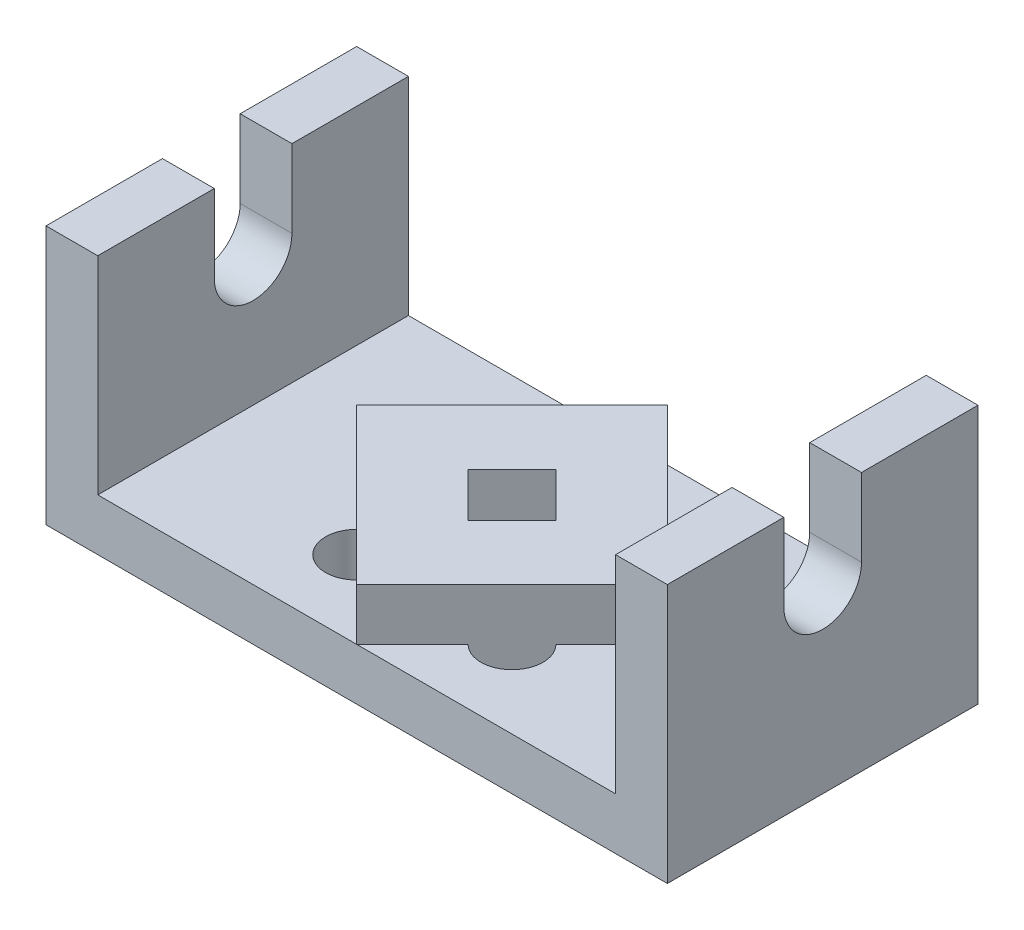
SolidWorks part; units mm, degrees
ref_plane "Front Plane" through (0, 0, 0) normal (0, 0, 1) x (1, 0, 0)
ref_plane "Top Plane" through (0, 0, 0) normal (0, 1, 0) x (1, 0, 0)
ref_plane "Right Plane" through (0, 0, 0) normal (1, 0, 0) x (0, 0, -1)
sketch "Sketch1" plane through (0, 0, 0) normal (0, 0, 1) x (1, 0, 0)
  line L0 (0, 44.72) -> (0, -57.36) construction
  line L1 (-92.16, 0) -> (92.8, 0) construction
  line L2 (-60, 0) -> (60, 0)
  line L3 (60, 0) -> (60, 50)
  line L4 (60, 50) -> (50, 50)
  line L5 (50, 50) -> (50, 10)
  line L6 (50, 10) -> (-50, 10)
  line L7 (-60, 50) -> (-50, 50)
  line L8 (-60, 0) -> (-60, 50)
  line L9 (-50, 50) -> (-50, 10)
  point P14 (0, 0)
  point P15 (0, 10)
  dimension "D1" = 60
  dimension "D2" = 50
  dimension "D3" = 10
  dimension "D4" = 10
extrude "Boss-Extrude1" add sketch "Sketch1" along normal mid plane 60
sketch "Sketch2" plane through (60, 0, 0) normal (1, 0, 0) x (0, 0, -1)
  line L0 (-30, 50) -> (30, 50) construction
  line L1 (-7.5, 35) -> (-7.5, 50)
  line L2 (7.5, 35) -> (7.5, 50)
  line L3 (-7.5, 50) -> (7.5, 50)
  arc A0 (-7.5, 35) -> (7.5, 35) centre (0, 35) ccw
  dimension "D1" = 15
  dimension "D2" = 15
extrude "Cut-Extrude1" cut sketch "Sketch2" against normal through all
sketch "Sketch3" plane through (0, 10, 0) normal (0, 1, 0) x (1, 0, 0)
  line L0 (0, 48.2725) -> (0, -50.768) construction
  line L1 (-75.801, 0) -> (79.5443, 0) construction
  line L2 (0, 30) -> (30, 0)
  line L3 (30, 0) -> (0, -30)
  line L4 (0, -30) -> (-30, 0)
  line L5 (-30, 0) -> (0, 30)
  point P7 (0, 0)
  dimension "D1" = 30
  dimension "D2" = 30
  dimension "D3" = 30
  dimension "D4" = 30
extrude "Boss-Extrude2" add sketch "Sketch3" along normal blind 10 contours L5 L2 L3 L4
sketch "Sketch4" plane through (0, 20, 0) normal (0, 1, 0) x (1, 0, 0)
  line L0 (0, 45.1531) -> (0, -53.2635) construction
  line L1 (-44.4512, 0) -> (42.8915, 0) construction
  line L2 (0, 8.4853) -> (8.4853, 0)
  line L3 (8.4853, 0) -> (0, -8.4853)
  line L4 (0, -8.4853) -> (-8.4853, 0)
  line L5 (-8.4853, 0) -> (0, 8.4853)
  dimension "D1" = 12
  dimension "D2" = 12
extrude "Cut-Extrude2" cut sketch "Sketch4" against normal through all
sketch "Sketch5" plane through (0, 20, 0) normal (0, 1, 0) x (1, 0, 0)
  line L0 (0, 41.5658) -> (0, -48.8963) construction
  line L1 (-44.1393, 0) -> (47.4146, 0) construction
  line L2 (0, 30) -> (30, 0) construction
  line L3 (0, 30) -> (30, 0) construction
  line L4 (10.7574, 19.2426) -> (19.2426, 10.7574)
  line L5 (19.2426, -10.7574) -> (10.7574, -19.2426)
  line L6 (-10.7574, -19.2426) -> (-19.2426, -10.7574)
  line L7 (-19.2426, 10.7574) -> (-10.7574, 19.2426)
  arc A0 (19.2426, 10.7574) -> (10.7574, 19.2426) centre (15, 15) ccw
  arc A1 (10.7574, -19.2426) -> (19.2426, -10.7574) centre (15, -15) ccw
  arc A2 (-19.2426, -10.7574) -> (-10.7574, -19.2426) centre (-15, -15) ccw
  arc A3 (-10.7574, 19.2426) -> (-19.2426, 10.7574) centre (-15, 15) ccw
  point P24 (0, 0)
  dimension "D1" = 6
  dimension "D2" = 4
extrude "Cut-Extrude3" cut sketch "Sketch5" against normal through all
